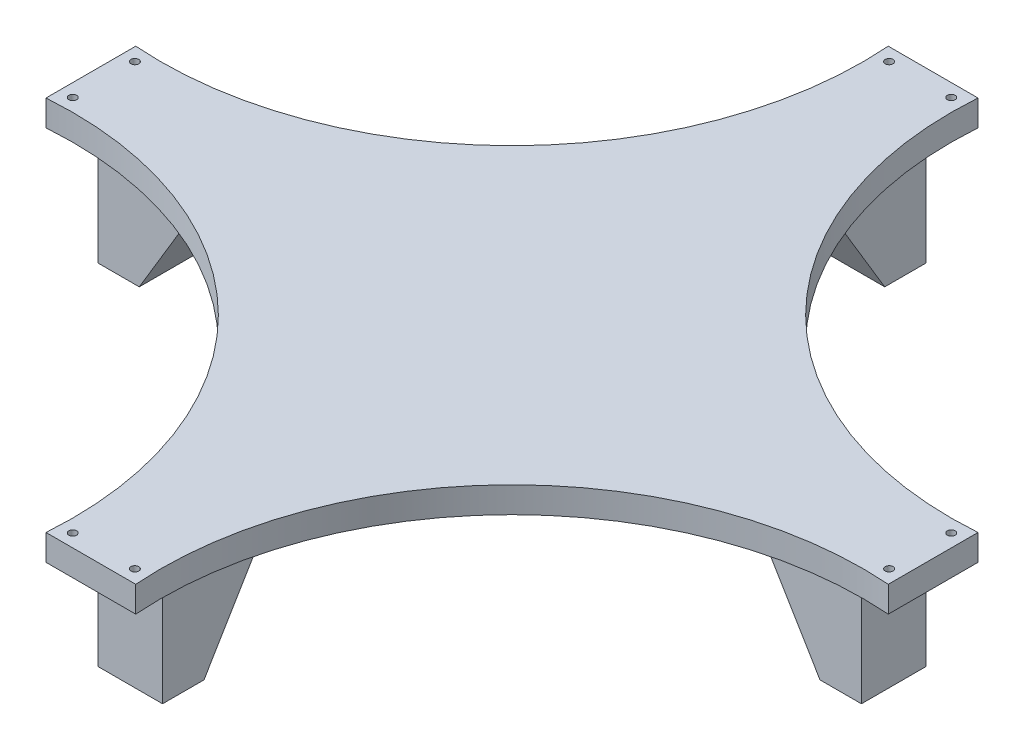
SolidWorks part; units mm, degrees
ref_plane "Front Plane" through (0, 0, 0) normal (0, 0, 1) x (1, 0, 0)
ref_plane "Top Plane" through (0, 0, 0) normal (0, 1, 0) x (1, 0, 0)
ref_plane "Right Plane" through (0, 0, 0) normal (1, 0, 0) x (0, 0, -1)
sketch "Sketch2" plane through (0, 0, 0) normal (0, 1, 0) x (1, 0, 0)
  line L0 (0, 0) -> (0, 152.66) construction
  line L1 (0, 0) -> (152.66, 0) construction
  line L2 (0, 152.66) -> (6.96, 152.66)
  line L3 (152.66, 0) -> (152.66, 6.96)
  line L4 (152.66, 0) -> (152.66, -6.96)
  line L5 (0, -152.66) -> (6.96, -152.66)
  line L6 (0, -152.66) -> (-6.96, -152.66)
  line L7 (-152.66, 0) -> (-152.66, -6.96)
  line L8 (-152.66, 0) -> (-152.66, 6.96)
  line L9 (0, 152.66) -> (-6.96, 152.66)
  line L10 (162.66, 0) -> (162.66, -17.329)
  line L11 (0, -162.66) -> (17.329, -162.66)
  line L12 (0, -162.66) -> (-17.329, -162.66)
  line L13 (-162.66, 0) -> (-162.66, -17.329)
  line L14 (-162.66, 0) -> (-162.66, 17.329)
  line L15 (0, 162.66) -> (-17.329, 162.66)
  line L16 (0, 162.66) -> (17.329, 162.66)
  line L17 (162.66, 0) -> (162.66, 17.329)
  line L18 (0, -162.66) -> (0, -152.66) construction
  line L19 (0, -157.66) -> (26.7486, -157.66) construction
  line L20 (0, -157.66) -> (-31.8023, -157.66) construction
  arc A0 (6.96, 152.66) -> (152.66, 6.96) centre (152.66, 152.66) ccw
  arc A1 (152.66, -6.96) -> (6.96, -152.66) centre (152.66, -152.66) ccw
  arc A2 (-6.96, -152.66) -> (-152.66, -6.96) centre (-152.66, -152.66) ccw
  arc A3 (-152.66, 6.96) -> (-6.96, 152.66) centre (-152.66, 152.66) ccw
  arc A4 (162.66, -17.329) -> (17.329, -162.66) centre (152.66, -152.66) ccw
  arc A5 (-17.329, -162.66) -> (-162.66, -17.329) centre (-152.66, -152.66) ccw
  arc A6 (-162.66, 17.329) -> (-17.329, 162.66) centre (-152.66, 152.66) ccw
  arc A7 (17.329, 162.66) -> (162.66, 17.329) centre (152.66, 152.66) ccw
  circle A8 centre (-12, -157.66) radius 1.5
  circle A9 centre (12, -157.66) radius 1.5
  circle A10 centre (-157.66, 12) radius 1.5
  circle A11 centre (-157.66, -12) radius 1.5
  circle A12 centre (12, 157.66) radius 1.5
  circle A13 centre (-12, 157.66) radius 1.5
  circle A14 centre (157.66, -12) radius 1.5
  circle A15 centre (157.66, 12) radius 1.5
  dimension "D6" = 3
  dimension "D7" = 3
  dimension "D1" = 152.66
  dimension "D2" = 152.66
  dimension "D3" = 6.96
  dimension "D8" = 12
  dimension "D9" = 12
  dimension "D5" = 10
  dimension "D4" = 4
  dimension "D10" = 4
extrude "Boss-Extrude1" add sketch "Sketch2" along normal blind 10 contours A7 L16 L15 A6 L14 L13 A5 L12 L11 A4 L10 L17 L8 A3 L9 L2 A0 L3 L4 A1 L5 L6 A2 L7 | A3 L8 L7 A2 L6 L5 A1 L4 L3 A0 L2 L9
sketch "Sketch3" plane through (0, 0, 0) normal (0, -1, 0) x (1, 0, 0)
  line L0 (17.329, 162.66) -> (-17.329, 162.66) construction
  line L1 (-162.66, 17.329) -> (-162.66, -17.329) construction
  line L2 (0, 162.66) -> (0, -162.66) construction
  line L3 (-17.329, -162.66) -> (17.329, -162.66) construction
  line L4 (-162.66, 0) -> (162.66, 0) construction
  line L5 (162.66, -17.329) -> (162.66, 17.329) construction
  line L6 (147.4657, -12.5) -> (147.4657, 12.5)
  line L7 (-147.4657, -12.5) -> (-107.4657, -12.5)
  line L8 (-147.4657, -12.5) -> (-147.4657, 12.5)
  line L9 (-147.4657, 12.5) -> (-107.4657, 12.5)
  line L10 (-107.4657, -12.5) -> (-107.4657, 12.5)
  line L11 (-147.4657, -12.5) -> (-107.4657, 12.5) construction
  line L12 (-147.4657, 12.5) -> (-107.4657, -12.5) construction
  line L13 (147.4657, 12.5) -> (107.4657, 12.5)
  line L14 (147.4657, -12.5) -> (107.4657, -12.5)
  line L15 (107.4657, -12.5) -> (107.4657, 12.5)
  line L16 (12.5, 147.4657) -> (12.5, 107.4657)
  line L17 (-12.5, 147.4657) -> (12.5, 147.4657)
  line L18 (-12.5, 147.4657) -> (-12.5, 107.4657)
  line L19 (-12.5, 107.4657) -> (12.5, 107.4657)
  line L20 (147.4657, -12.5) -> (107.4657, -12.5)
  line L21 (147.4657, 12.5) -> (147.4657, -12.5)
  line L22 (147.4657, 12.5) -> (107.4657, 12.5)
  line L23 (107.4657, 12.5) -> (107.4657, -12.5)
  line L24 (-12.5, -147.4657) -> (-12.5, -107.4657)
  line L25 (12.5, -147.4657) -> (-12.5, -147.4657)
  line L26 (12.5, -147.4657) -> (12.5, -107.4657)
  line L27 (12.5, -107.4657) -> (-12.5, -107.4657)
  point P0 (0, 162.66)
  point P1 (-162.66, 0)
  point P14 (-127.4657, 0)
  dimension "D1" = 40
  dimension "D2" = 25
  dimension "D3" = 4
extrude "Boss-Extrude2" add sketch "Sketch3" along normal blind 40 contours L18 L19 L16 L17 | L15 L14 L6 L13 | L26 L27 L24 L25 | L7 L10 L9 L8
sketch "Sketch4" plane through (0, 0, -12.5) normal (0, 0, -1) x (-1, 0, 0)
  line L0 (-131.4657, -40) -> (-107.4657, 0)
  line L1 (-147.4657, -40) -> (-107.4657, -40) construction
  line L2 (-107.4657, -40) -> (-107.4657, 0) construction
  line L4 (-131.4657, -40) -> (-107.4657, -40)
  line L5 (-107.4657, -40) -> (-107.4657, 0)
  dimension "D1" = 16
extrude "Cut-Extrude1" cut sketch "Sketch4" against normal blind 40
pattern_circular "CirPattern1" count 4 over 360 about axis through (0, 0, 0) along (0, 1, 0) of "Cut-Extrude1"
